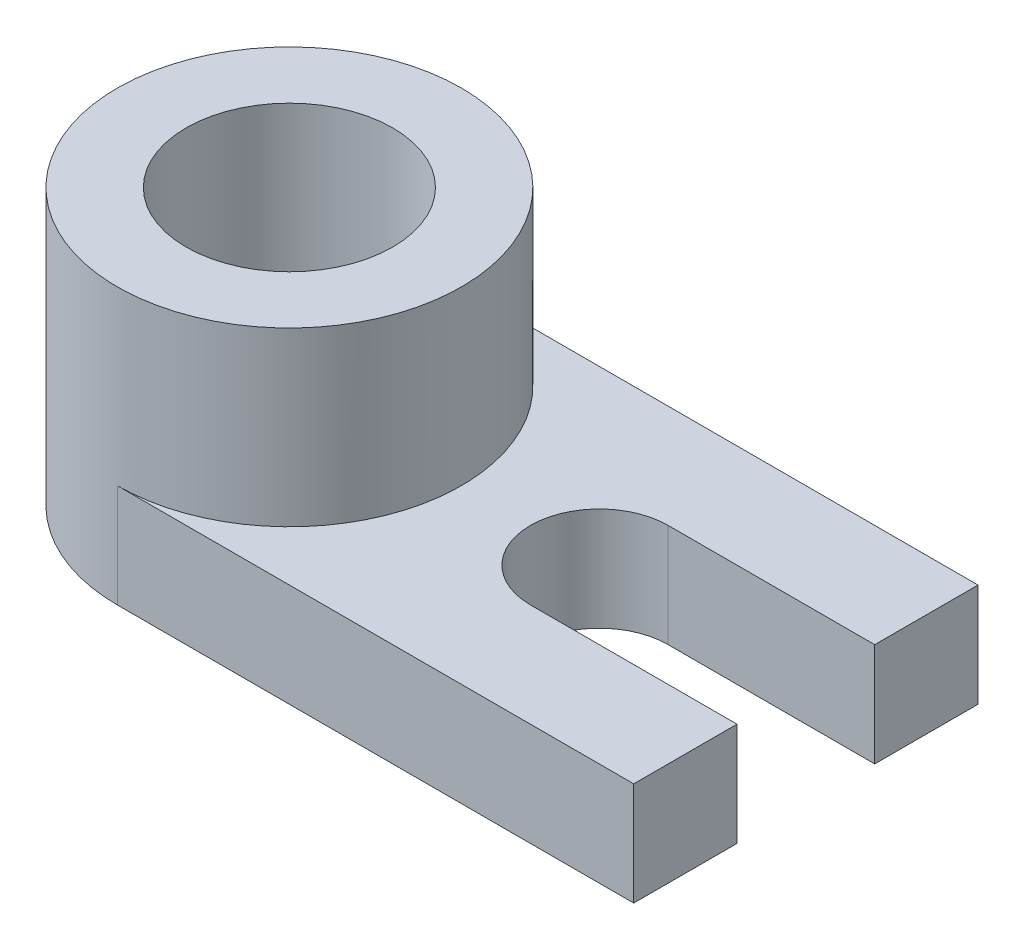
SolidWorks part; units mm, degrees
ref_plane "Front Plane" through (0, 0, 0) normal (0, 0, 1) x (1, 0, 0)
ref_plane "Top Plane" through (0, 0, 0) normal (0, 1, 0) x (1, 0, 0)
ref_plane "Right Plane" through (0, 0, 0) normal (1, 0, 0) x (0, 0, -1)
sketch "Sketch1" plane through (0, 0, 0) normal (0, 1, 0) x (1, 0, 0)
  line L1 (0, 0) -> (75, 0)
  line L2 (0, 0) -> (0, 50)
  line L3 (0, 50) -> (75, 50)
  line L4 (75, 0) -> (75, 50)
  dimension "D1" = 75
  dimension "D2" = 50
extrude "Boss-Extrude1" add sketch "Sketch1" along normal blind 15
sketch "Sketch2" plane through (0, 0, 0) normal (0, -1, 0) x (1, 0, 0)
  line L0 (0, -50) -> (0, 0) construction
  circle A0 centre (0, -25) radius 25
extrude "Boss-Extrude2" add sketch "Sketch2" against normal blind 40
sketch "Sketch3" plane through (0, 40, 0) normal (0, 1, 0) x (1, 0, 0)
  circle A0 centre (0, 25) radius 15
  dimension "D1" = 30
extrude "Cut-Extrude1" cut sketch "Sketch3" against normal through all
sketch "Sketch4" plane through (0, 15, 0) normal (0, 1, 0) x (1, 0, 0)
  line L0 (75, 0) -> (75, 50) construction
  line L1 (75, 50) -> (0, 50) construction
  circle A0 centre (45, 25) radius 10
  dimension "D3" = 20
  dimension "D1" = 30
  dimension "D2" = 25
extrude "Cut-Extrude2" cut sketch "Sketch4" against normal through all
sketch "Sketch5" plane through (75, 0, 0) normal (1, 0, 0) x (0, 0, -1)
  line L0 (0, 15) -> (50, 15) construction
  line L1 (15, 15) -> (35, 15)
  line L2 (15, 15) -> (15, 0)
  line L3 (15, 0) -> (35, 0)
  line L4 (35, 15) -> (35, 0)
  line L5 (0, 0) -> (50, 0) construction
  line L6 (0, 15) -> (0, 0) construction
  line L7 (50, 15) -> (50, 0) construction
  dimension "D1" = 15
  dimension "D2" = 15
extrude "Cut-Extrude3" cut sketch "Sketch5" against normal up to next
